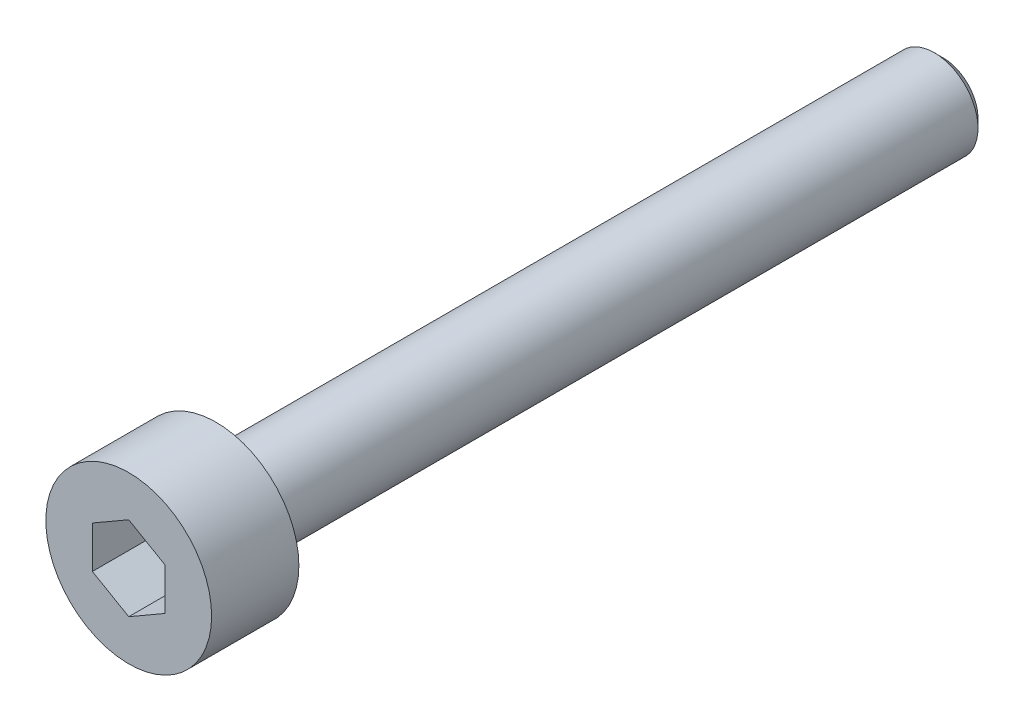
SolidWorks part; units mm, degrees
ref_plane "Front Plane" through (0, 0, 0) normal (0, 0, 1) x (1, 0, 0)
ref_plane "Top Plane" through (0, 0, 0) normal (0, 1, 0) x (1, 0, 0)
ref_plane "Right Plane" through (0, 0, 0) normal (1, 0, 0) x (0, 0, -1)
sketch "Sketch1" plane through (0, 0, 0) normal (0, 0, 1) x (1, 0, 0)
  circle A0 centre (0, 0) radius 2.85
  dimension "D1" = 5.7
extrude "Boss-Extrude1" add sketch "Sketch1" along normal blind 3
sketch "Sketch2" plane through (0, 0, 0) normal (0, 0, -1) x (-1, 0, 0)
  circle A0 centre (0, 0) radius 1.5
  dimension "D1" = 3
extrude "Boss-Extrude2" add sketch "Sketch2" along normal blind 25
chamfer "Chamfer1" distance 0.3 angle 45 1 edges at (-1.5, 0, -25)
sketch "Sketch3" plane through (0, 0, 3) normal (0, 0, 1) x (1, 0, 0)
  line L1 (0, 1.4434) -> (-1.25, 0.7217)
  line L2 (-1.25, 0.7217) -> (-1.25, -0.7217)
  line L3 (-1.25, -0.7217) -> (0, -1.4434)
  line L4 (0, -1.4434) -> (1.25, -0.7217)
  line L5 (1.25, -0.7217) -> (1.25, 0.7217)
  line L6 (1.25, 0.7217) -> (0, 1.4434)
  circle A0 centre (0, 0) radius 1.25 construction
  dimension "D1" = 2.5
extrude "Cut-Extrude1" cut sketch "Sketch3" against normal blind 2
